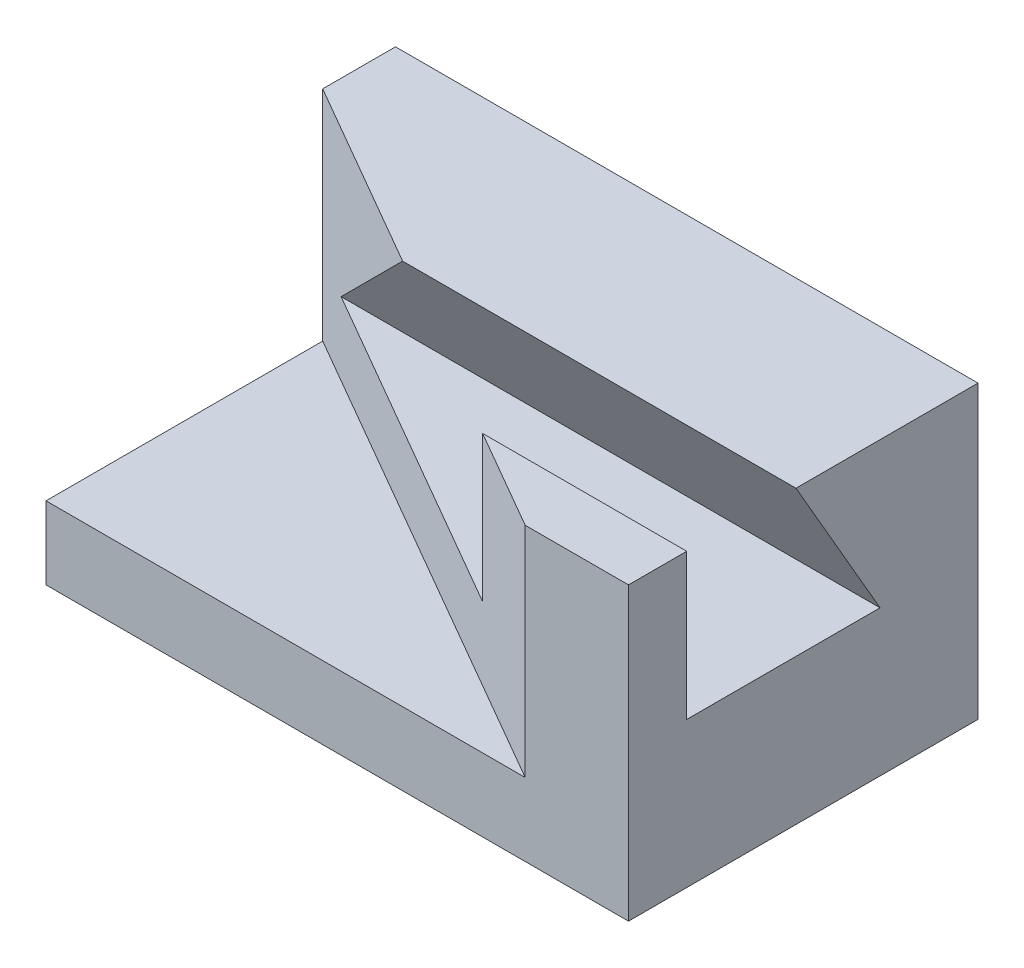
SolidWorks part; units mm, degrees
ref_plane "Ebene vorne" through (0, 0, 0) normal (0, 0, 1) x (1, 0, 0)
ref_plane "Ebene oben" through (0, 0, 0) normal (0, 1, 0) x (1, 0, 0)
ref_plane "Ebene rechts" through (0, 0, 0) normal (1, 0, 0) x (0, 0, -1)
sketch "Skizze1" plane through (0, 0, 0) normal (0, 1, 0) x (1, 0, 0)
  line L1 (0, 0) -> (-80, 0)
  line L2 (0, 0) -> (0, 48)
  line L3 (0, 48) -> (-80, 48)
  line L4 (-80, 0) -> (-80, 48)
  dimension "D1" = 48
  dimension "D2" = 80
extrude "Aufsatz-Linear austragen1" add sketch "Skizze1" along normal blind 40
sketch "Skizze2" plane through (0, 40, 0) normal (0, 1, 0) x (1, 0, 0)
  line L0 (-80, 0) -> (-80, 38)
  line L1 (-80, 48) -> (-80, 0) construction
  line L2 (-80, 38) -> (-14.1821, 0)
  line L3 (-80, 0) -> (0, 0) construction
  line L4 (-14.1821, 0) -> (-80, 0)
  dimension "D1" = 60
  dimension "D2" = 38
extrude "Schnitt-Linear austragen1" cut sketch "Skizze2" against normal blind 30
sketch "Skizze4" plane through (0, 0, 0) normal (1, 0, 0) x (0, 0, -1)
  line L0 (23, 40) -> (34.547, 20)
  line L1 (0, 40) -> (48, 40) construction
  line L2 (34.547, 20) -> (8, 20)
  line L3 (8, 20) -> (8, 40)
  line L4 (8, 40) -> (23, 40)
  line L5 (0, 40) -> (0, 0) construction
  dimension "D1" = 15
  dimension "D2" = 60
  dimension "D3" = 8
  dimension "D4" = 20
extrude "Schnitt-Linear austragen2" cut sketch "Skizze4" against normal through all
